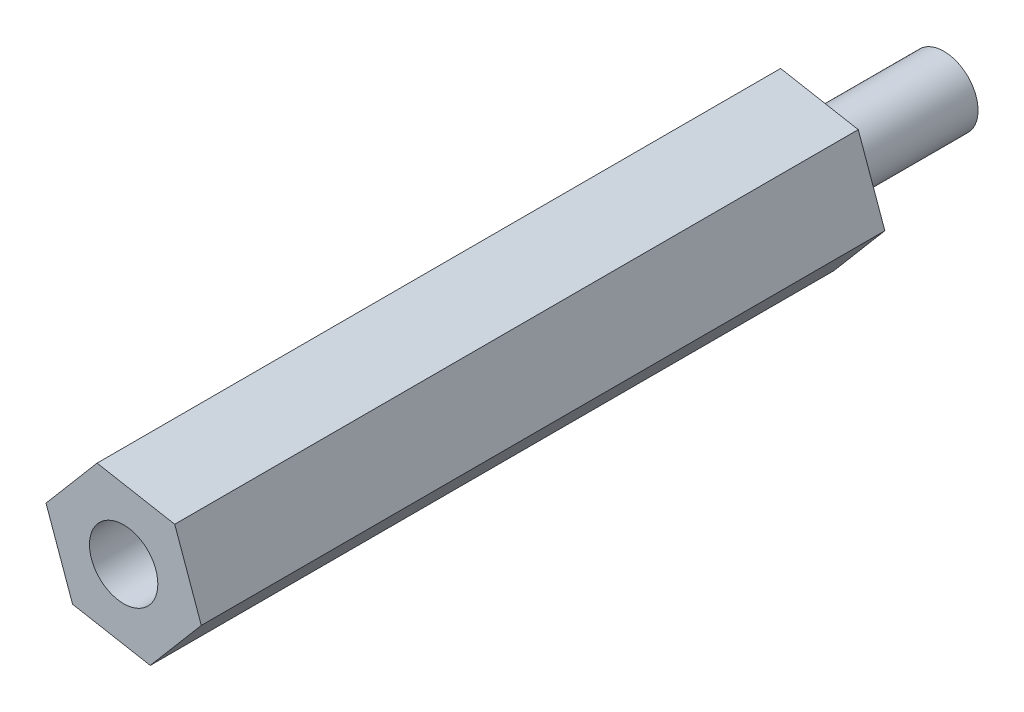
SolidWorks part; units mm, degrees
material "ABS"
ref_plane "Plano frontal" through (0, 0, 0) normal (0, 0, 1) x (1, 0, 0)
ref_plane "Plano superior" through (0, 0, 0) normal (0, 1, 0) x (1, 0, 0)
ref_plane "Plano direito" through (0, 0, 0) normal (1, 0, 0) x (0, 0, -1)
sketch "Esboço1" plane through (0, 0, 0) normal (0, 0, 1) x (1, 0, 0)
  line L1 (12.9332, -4.1439) -> (9.5251, -3.5237)
  line L2 (9.5251, -3.5237) -> (7.2839, -6.1651)
  line L3 (7.2839, -6.1651) -> (8.4508, -9.4267)
  line L4 (8.4508, -9.4267) -> (11.8589, -10.0469)
  line L5 (11.8589, -10.0469) -> (14.1001, -7.4055)
  line L6 (14.1001, -7.4055) -> (12.9332, -4.1439)
  circle A0 centre (10.692, -6.7853) radius 3 construction
extrude "Ressalto-extrusão1" add sketch "Esboço1" along normal blind 30
sketch "Esboço4" plane through (0, 0, 0) normal (0, 0, -1) x (-1, 0, 0)
  line L1 (-12.9332, -4.1439) -> (-9.5251, -3.5237) construction
  circle A0 centre (-10.692, -6.7853) radius 1.5
  dimension "D1" = 3
extrude "Corte-extrusão2" cut sketch "Esboço4" against normal blind 40
sketch "Esboço6" plane through (0, 0, 0) normal (0, 0, -1) x (-1, 0, 0)
  circle A0 centre (-10.692, -6.7853) radius 1.5
  dimension "D1" = 3
extrude "Ressalto-extrusão2" add sketch "Esboço6" along normal blind 6 separate body
